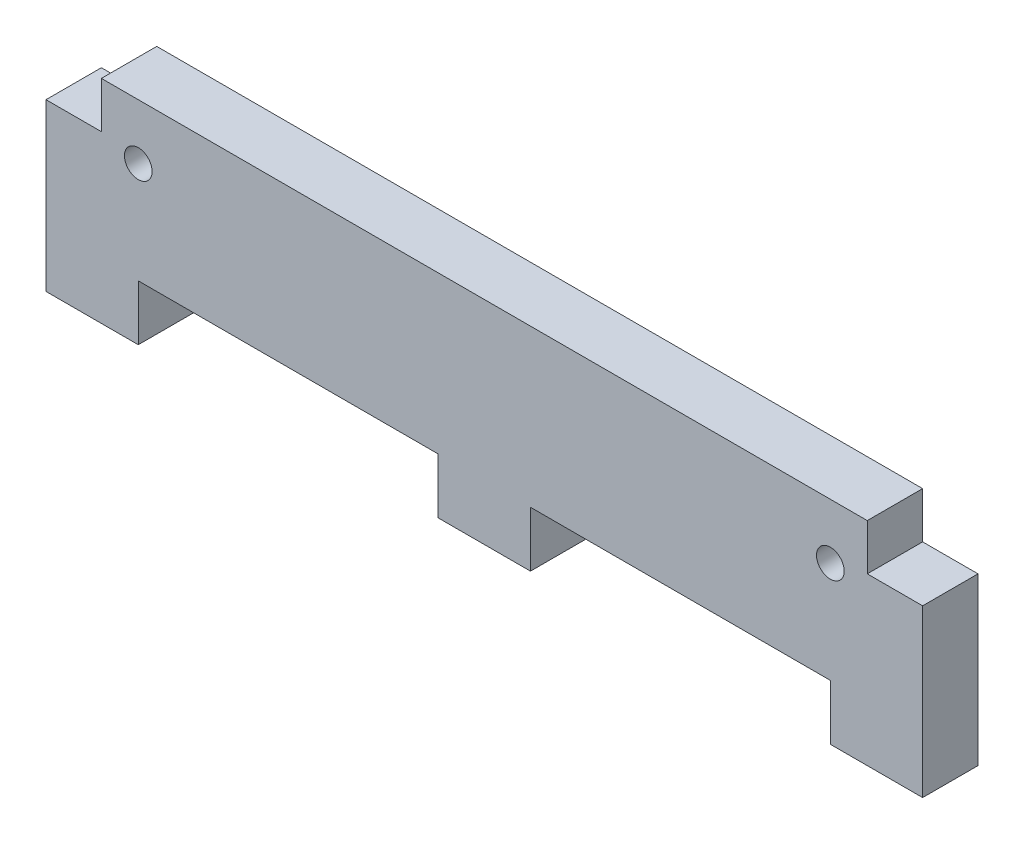
SolidWorks part; units mm, degrees
material "Acrylic (Medium-high impact)"
ref_plane "Front Plane" through (0, 0, 0) normal (0, 0, 1) x (1, 0, 0)
ref_plane "Top Plane" through (0, 0, 0) normal (0, 1, 0) x (1, 0, 0)
ref_plane "Right Plane" through (0, 0, 0) normal (1, 0, 0) x (0, 0, -1)
sketch "Sketch1" plane through (0, 0, 0) normal (0, 0, 1) x (1, 0, 0)
  line L1 (0, 0) -> (95, 0)
  line L2 (0, 0) -> (0, 23)
  line L3 (0, 23) -> (95, 23)
  line L4 (95, 0) -> (95, 23)
  dimension "D1" = 23
  dimension "D2" = 95
extrude "Boss-Extrude1" add sketch "Sketch1" along normal blind 6
sketch "Sketch2" plane through (0, 0, 6) normal (0, 0, 1) x (1, 0, 0)
  line L0 (0, 0) -> (95, 0) construction
  line L1 (10, 0) -> (42.5, 0)
  line L2 (10, 0) -> (10, 6)
  line L3 (10, 6) -> (42.5, 6)
  line L4 (42.5, 0) -> (42.5, 6)
  line L5 (0, 23) -> (0, 0) construction
  line L6 (52.5, 0) -> (85, 0)
  line L7 (52.5, 0) -> (52.5, 6)
  line L8 (52.5, 6) -> (85, 6)
  line L9 (85, 0) -> (85, 6)
  line L10 (95, 0) -> (95, 23) construction
  dimension "D1" = 10
  dimension "D2" = 6
  dimension "D3" = 10
  dimension "D4" = 10
extrude "Cut-Extrude1" cut sketch "Sketch2" against normal through all
sketch "Sketch4" plane through (0, 0, 6) normal (0, 0, 1) x (1, 0, 0)
  line L0 (95, 23) -> (0, 23) construction
  line L1 (0, 23) -> (0, 0) construction
  line L2 (95, 0) -> (95, 23) construction
  circle A0 centre (10, 17) radius 1.5
  circle A1 centre (85, 17) radius 1.5
  dimension "D1" = 3
  dimension "D4" = 6
  dimension "D5" = 10
  dimension "D2" = 6
  dimension "D3" = 10
extrude "Cut-Extrude2" cut sketch "Sketch4" against normal through all
sketch "Sketch5" plane through (0, 0, 6) normal (0, 0, 1) x (1, 0, 0)
  line L1 (0, 23) -> (6, 23)
  line L2 (0, 23) -> (0, 18)
  line L3 (0, 18) -> (6, 18)
  line L4 (6, 23) -> (6, 18)
  line L5 (95, 23) -> (89, 23)
  line L6 (95, 23) -> (95, 18)
  line L7 (95, 18) -> (89, 18)
  line L8 (89, 23) -> (89, 18)
  dimension "D1" = 6
  dimension "D2" = 5
extrude "Cut-Extrude3" cut sketch "Sketch5" against normal through all
